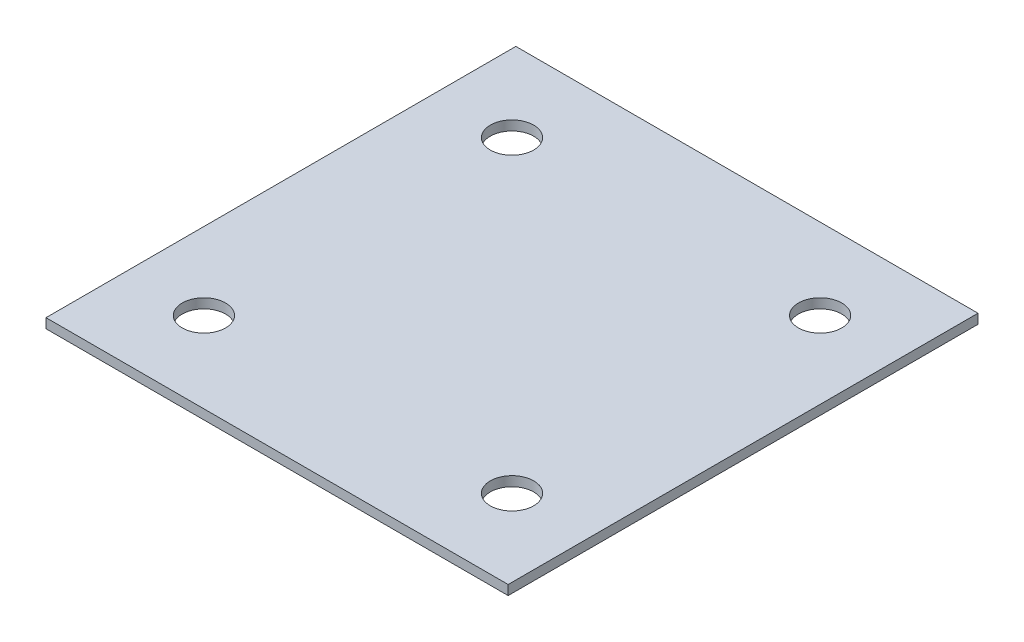
SolidWorks part; units mm, degrees
ref_plane "Front Plane" through (0, 0, 0) normal (0, 0, 1) x (1, 0, 0)
ref_plane "Top Plane" through (0, 0, 0) normal (0, 1, 0) x (1, 0, 0)
ref_plane "Right Plane" through (0, 0, 0) normal (1, 0, 0) x (0, 0, -1)
sketch "Sketch1" plane through (0, 0, 0) normal (0, 1, 0) x (1, 0, 0)
  line L1 (0, 0) -> (304.8, 0)
  line L2 (0, 0) -> (0, 309.88)
  line L3 (0, 309.88) -> (304.8, 309.88)
  line L4 (304.8, 0) -> (304.8, 309.88)
  circle A0 centre (50.8, 53.34) radius 14.2875
  circle A1 centre (254, 53.34) radius 14.2875
  circle A2 centre (50.8, 256.54) radius 14.2875
  circle A3 centre (254, 256.54) radius 14.2875
  circle A4 centre (50.8, 256.54) radius 50.8 construction
  circle A5 centre (254, 256.54) radius 50.8 construction
  circle A6 centre (254, 53.34) radius 50.8 construction
  circle A7 centre (50.8, 53.34) radius 50.8 construction
  point P16 (0, 199.35)
  point P18 (293.639, 0)
  point P19 (231.9194, 150.527)
  point P20 (396.7438, 288.8031)
  point P21 (247.1133, 237.2283)
  point P22 (304.8, 311.7252)
  point P23 (254, 52.5779)
  dimension "D1" = 28.575
  dimension "D2" = 101.6
  dimension "D3" = 101.6
  dimension "D5" = 2.54
  dimension "D4" = 304.8
  dimension "D6" = 2.54
extrude "Boss-Extrude1" add sketch "Sketch1" along normal mid plane 6.35
